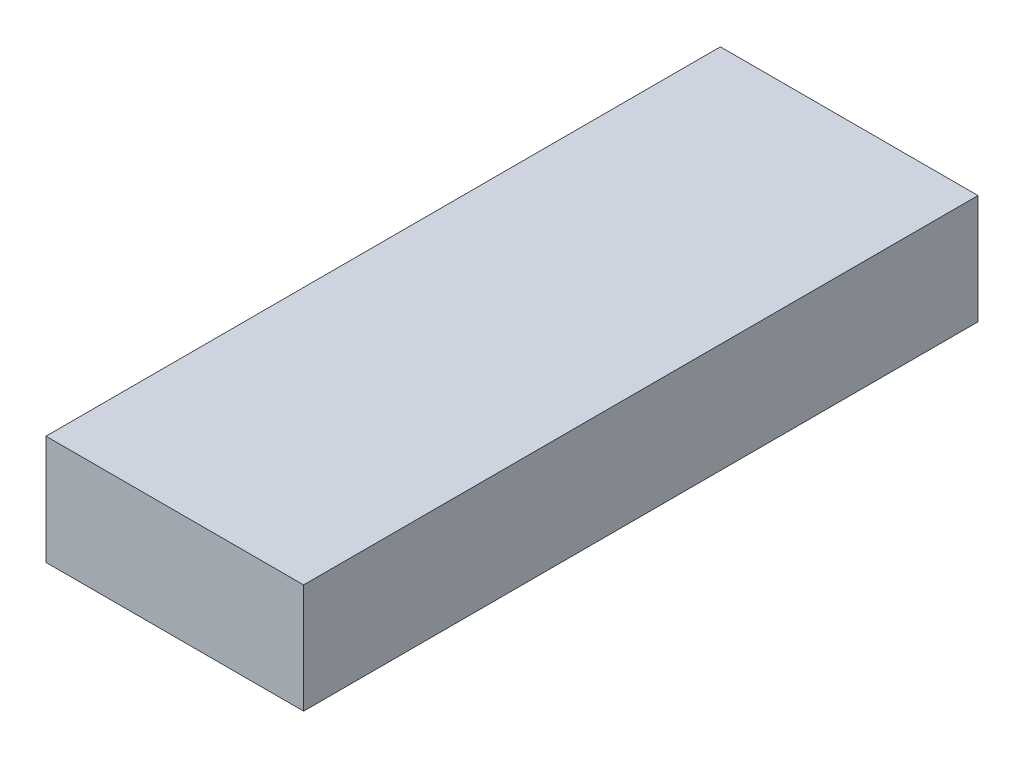
SolidWorks part; units mm, degrees
ref_plane "Front Plane" through (0, 0, 0) normal (0, 0, 1) x (1, 0, 0)
ref_plane "Top Plane" through (0, 0, 0) normal (0, 1, 0) x (1, 0, 0)
ref_plane "Right Plane" through (0, 0, 0) normal (1, 0, 0) x (0, 0, -1)
other "Bounding Box"
ref_plane "Default Plane" through (13.8565, 3.175, 6.7999) normal (0, -1, 0) x (-1, 0, 0)
sketch "Sketch1" plane through (0, 0, 0) normal (0, 1, 0) x (1, 0, 0)
  line L1 (-13.462, -35.2425) -> (13.462, -35.2425)
  line L2 (-13.462, -35.2425) -> (-13.462, 35.2425)
  line L3 (-13.462, 35.2425) -> (13.462, 35.2425)
  line L4 (13.462, -35.2425) -> (13.462, 35.2425)
  line L5 (-13.462, -35.2425) -> (13.462, 35.2425) construction
  line L6 (-13.462, 35.2425) -> (13.462, -35.2425) construction
  point P0 (0, 0)
  dimension "D1" = 26.924
  dimension "D2" = 70.485
extrude "Boss-Extrude1" add sketch "Sketch1" along normal mid plane 11.43
